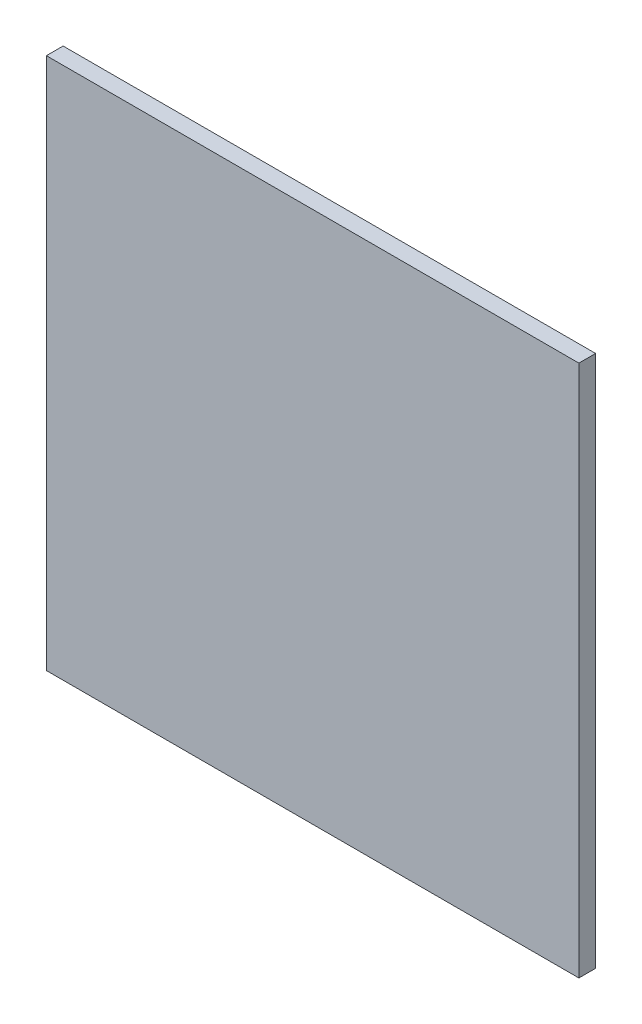
SolidWorks part; units mm, degrees
ref_plane "前视基准面" through (0, 0, 0) normal (0, 0, 1) x (1, 0, 0)
ref_plane "上视基准面" through (0, 0, 0) normal (0, 1, 0) x (1, 0, 0)
ref_plane "右视基准面" through (0, 0, 0) normal (1, 0, 0) x (0, 0, -1)
sketch "草图1" plane through (0, 0, 0) normal (0, 0, 1) x (1, 0, 0)
  line L1 (-17.5, -17.5) -> (17.5, -17.5)
  line L2 (-17.5, -17.5) -> (-17.5, 17.5)
  line L3 (-17.5, 17.5) -> (17.5, 17.5)
  line L4 (17.5, -17.5) -> (17.5, 17.5)
  line L5 (-17.5, -17.5) -> (17.5, 17.5) construction
  line L6 (-17.5, 17.5) -> (17.5, -17.5) construction
  circle A0 centre (0, 0) radius 8.75 construction
  dimension "D1" = 17.5
  dimension "D2" = 35
  dimension "D3" = 35
extrude "凸台-拉伸1" add sketch "草图1" along normal blind 1.1
